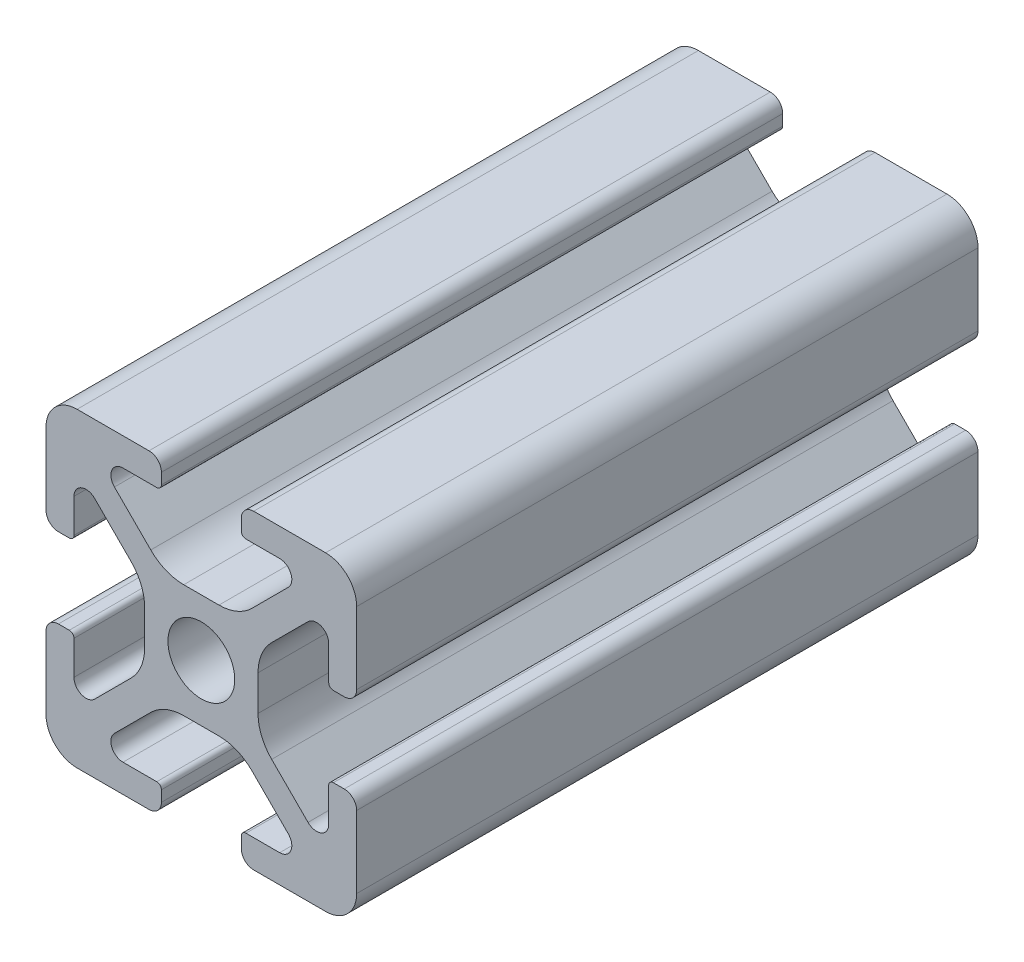
SolidWorks part; units mm, degrees
ref_plane "Alzado" through (0, 0, 0) normal (0, 0, 1) x (1, 0, 0)
ref_plane "Planta" through (0, 0, 0) normal (0, 1, 0) x (1, 0, 0)
ref_plane "Vista lateral" through (0, 0, 0) normal (1, 0, 0) x (0, 0, -1)
sketch "Croquis1" plane through (0, 0, 0) normal (0, 0, 1) x (1, 0, 0)
  line L0 (3.65, 1.1346) -> (3.65, -1.1346)
  line L1 (4.5287, 3.2559) -> (6.8685, 5.5957)
  line L2 (8.2, 2.87) -> (8.2, 5.0441)
  line L3 (3.2559, 4.5287) -> (5.5957, 6.8685)
  line L4 (2.87, 8.2) -> (5.0441, 8.2)
  line L5 (9.2, 2.57) -> (8.5, 2.57)
  line L6 (2.57, 9.2) -> (2.57, 8.5)
  line L7 (10, 8) -> (10, 3.37)
  line L8 (8, 10) -> (3.37, 10)
  line L9 (-1.1346, -3.65) -> (1.1346, -3.65)
  line L10 (-4.5287, -3.2559) -> (-6.8685, -5.5957)
  line L11 (-8.2, -2.87) -> (-8.2, -5.0441)
  line L12 (-3.2559, -4.5287) -> (-5.5957, -6.8685)
  line L13 (-2.87, -8.2) -> (-5.0441, -8.2)
  line L14 (-9.2, -2.57) -> (-8.5, -2.57)
  line L15 (-2.57, -9.2) -> (-2.57, -8.5)
  line L16 (-10, -8) -> (-10, -3.37)
  line L17 (-8, -10) -> (-3.37, -10)
  line L18 (8, -10) -> (3.37, -10)
  line L19 (10, -8) -> (10, -3.37)
  line L20 (2.57, -9.2) -> (2.57, -8.5)
  line L21 (9.2, -2.57) -> (8.5, -2.57)
  line L22 (2.87, -8.2) -> (5.0441, -8.2)
  line L23 (3.2559, -4.5287) -> (5.5957, -6.8685)
  line L24 (8.2, -2.87) -> (8.2, -5.0441)
  line L25 (4.5287, -3.2559) -> (6.8685, -5.5957)
  line L36 (0, 14.6478) -> (0, -3.65) construction
  line L37 (3.65, 0) -> (-17.4085, 0) construction
  line L40 (0, 0) -> (-13.7486, 13.7486) construction
  line L41 (-8, 10) -> (-3.37, 10)
  line L42 (-10, 8) -> (-10, 3.37)
  line L43 (-2.57, 9.2) -> (-2.57, 8.5)
  line L44 (-9.2, 2.57) -> (-8.5, 2.57)
  line L45 (-2.87, 8.2) -> (-5.0441, 8.2)
  line L46 (-3.2559, 4.5287) -> (-5.5957, 6.8685)
  line L47 (-8.2, 2.87) -> (-8.2, 5.0441)
  line L48 (-4.5287, 3.2559) -> (-6.8685, 5.5957)
  line L49 (-1.1346, 3.65) -> (1.1346, 3.65)
  line L51 (-3.65, 1.1346) -> (-3.65, -1.1346)
  arc A0 (6.8685, 5.5957) -> (8.2, 5.0441) centre (7.42, 5.0441) cw
  arc A1 (5.5957, 6.8685) -> (5.0441, 8.2) centre (5.0441, 7.42) ccw
  arc A2 (4.5287, 3.2559) -> (3.65, 1.1346) centre (6.65, 1.1346) ccw
  arc A3 (3.2559, 4.5287) -> (1.1346, 3.65) centre (1.1346, 6.65) cw
  arc A4 (8.5, 2.57) -> (8.2, 2.87) centre (8.5, 2.87) cw
  arc A5 (2.87, 8.2) -> (2.57, 8.5) centre (2.87, 8.5) cw
  arc A6 (3.37, 10) -> (2.57, 9.2) centre (3.37, 9.2) ccw
  arc A7 (10, 3.37) -> (9.2, 2.57) centre (9.2, 3.37) cw
  arc A8 (8, 10) -> (10, 8) centre (8, 8) cw
  arc A9 (-6.8685, -5.5957) -> (-8.2, -5.0441) centre (-7.42, -5.0441) cw
  arc A10 (-5.5957, -6.8685) -> (-5.0441, -8.2) centre (-5.0441, -7.42) ccw
  arc A11 (-4.5287, -3.2559) -> (-3.65, -1.1346) centre (-6.65, -1.1346) ccw
  arc A12 (-3.2559, -4.5287) -> (-1.1346, -3.65) centre (-1.1346, -6.65) cw
  arc A13 (-8.5, -2.57) -> (-8.2, -2.87) centre (-8.5, -2.87) cw
  arc A14 (-2.87, -8.2) -> (-2.57, -8.5) centre (-2.87, -8.5) cw
  arc A15 (-3.37, -10) -> (-2.57, -9.2) centre (-3.37, -9.2) ccw
  arc A16 (-10, -3.37) -> (-9.2, -2.57) centre (-9.2, -3.37) cw
  arc A17 (-8, -10) -> (-10, -8) centre (-8, -8) cw
  arc A18 (8, -10) -> (10, -8) centre (8, -8) ccw
  arc A19 (10, -3.37) -> (9.2, -2.57) centre (9.2, -3.37) ccw
  arc A20 (3.37, -10) -> (2.57, -9.2) centre (3.37, -9.2) cw
  arc A21 (2.87, -8.2) -> (2.57, -8.5) centre (2.87, -8.5) ccw
  arc A22 (8.5, -2.57) -> (8.2, -2.87) centre (8.5, -2.87) ccw
  arc A23 (3.2559, -4.5287) -> (1.1346, -3.65) centre (1.1346, -6.65) ccw
  arc A24 (4.5287, -3.2559) -> (3.65, -1.1346) centre (6.65, -1.1346) cw
  arc A25 (5.5957, -6.8685) -> (5.0441, -8.2) centre (5.0441, -7.42) cw
  arc A26 (6.8685, -5.5957) -> (8.2, -5.0441) centre (7.42, -5.0441) ccw
  circle A33 centre (0, 0) radius 2.15
  arc A37 (-8, 10) -> (-10, 8) centre (-8, 8) ccw
  arc A38 (-10, 3.37) -> (-9.2, 2.57) centre (-9.2, 3.37) ccw
  arc A39 (-3.37, 10) -> (-2.57, 9.2) centre (-3.37, 9.2) cw
  arc A40 (-2.87, 8.2) -> (-2.57, 8.5) centre (-2.87, 8.5) ccw
  arc A41 (-8.5, 2.57) -> (-8.2, 2.87) centre (-8.5, 2.87) ccw
  arc A42 (-3.2559, 4.5287) -> (-1.1346, 3.65) centre (-1.1346, 6.65) ccw
  arc A43 (-4.5287, 3.2559) -> (-3.65, 1.1346) centre (-6.65, 1.1346) cw
  arc A44 (-5.5957, 6.8685) -> (-5.0441, 8.2) centre (-5.0441, 7.42) cw
  arc A45 (-6.8685, 5.5957) -> (-8.2, 5.0441) centre (-7.42, 5.0441) ccw
  point P27 (0, 3.65)
  point P28 (8.2, 6.9272)
  point P29 (6.9272, 8.2)
  point P30 (3.65, 2.3772)
  point P31 (2.3772, 3.65)
  point P32 (10, 10)
  point P87 (-3.65, 0)
  point P88 (-8.2, -6.9272)
  point P89 (-6.9272, -8.2)
  point P90 (-3.65, -2.3772)
  point P91 (-2.3772, -3.65)
  point P92 (-10, -10)
  point P93 (10, -10)
  point P94 (2.3772, -3.65)
  point P95 (3.65, -2.3772)
  point P96 (6.9272, -8.2)
  point P97 (8.2, -6.9272)
  point P127 (-10, 10)
  point P149 (-2.3772, 3.65)
  point P152 (-3.65, 2.3772)
  point P154 (-6.9272, 8.2)
  point P156 (-8.2, 6.9272)
  dimension "D2" = 4.3
  dimension "D6" = 10
  dimension "D15" = 0.3
  dimension "D17" = 0.9
  dimension "D10" = 2
  dimension "D13" = 0.8
  dimension "D21" = 0.3
  dimension "D25" = 3
  dimension "D26" = 3
  dimension "D27" = 0.78
  dimension "D29" = 0.78
  dimension "D4" = 10
  dimension "D14" = 1.8
  dimension "D22" = 3.65
  dimension "D28" = 7.43
extrude "Saliente-Extruir1" add sketch "Croquis1" along normal blind 40
